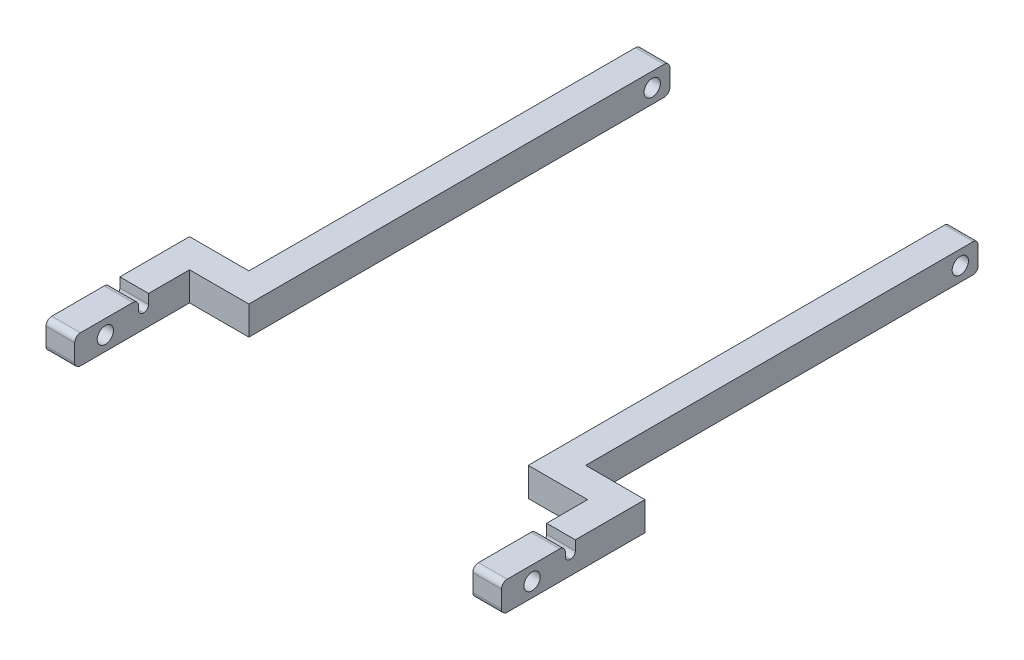
SolidWorks part; units mm, degrees
material "Custom Plastic"
ref_plane "Front Plane" through (0, 0, 0) normal (0, 0, 1) x (1, 0, 0)
ref_plane "Top Plane" through (0, 0, 0) normal (0, 1, 0) x (1, 0, 0)
ref_plane "Right Plane" through (0, 0, 0) normal (1, 0, 0) x (0, 0, -1)
sketch "Sketch2" plane through (0, 0, 0) normal (0, 1, 0) x (1, 0, 0)
  line L0 (130, 280) -> (145, 280)
  line L1 (0, 0) -> (15, 0) construction
  line L2 (0, 75) -> (0, 280)
  line L3 (0, 280) -> (15, 280)
  line L4 (176, 75) -> (176, 280)
  line L6 (46, 280) -> (46, 240)
  line L8 (130, 280) -> (130, 240)
  line L11 (31, 240) -> (31, 280)
  line L15 (145, 240) -> (145, 280)
  line L16 (31, 280) -> (46, 280)
  line L17 (161, 280) -> (176, 280)
  line L25 (130, 240) -> (46, 240)
  line L26 (31, 240) -> (31, 225)
  line L30 (161, 0) -> (176, 0) construction
  line L31 (145, 240) -> (145, 225)
  line L34 (31, 225) -> (145, 225)
  line L35 (15, 280) -> (15, 60)
  line L36 (161, 280) -> (161, 60)
  line L37 (15, 60) -> (-16, 60)
  line L44 (-16, 60) -> (-16, 0)
  line L45 (-16, 0) -> (-31, 0)
  line L46 (-31, 0) -> (-31, 75)
  line L47 (-31, 75) -> (0, 75)
  line L48 (0, 0) -> (0, 60) construction
  line L49 (15, 60) -> (15, 0) construction
  line L50 (0, 60) -> (0, 75) construction
  line L51 (88, 240) -> (88, 0) construction
  line L52 (192, 0) -> (207, 0)
  line L53 (192, 60) -> (192, 0)
  line L54 (161, 60) -> (192, 60)
  line L55 (207, 0) -> (207, 75)
  line L56 (207, 75) -> (176, 75)
  line L57 (176, 0) -> (176, 60) construction
  line L58 (161, 60) -> (161, 0) construction
  line L59 (176, 60) -> (176, 75) construction
  point P6 (31, 260)
  point P36 (0, 0)
  dimension "D2" = 280
  dimension "D3" = 16
  dimension "D4" = 114
  dimension "D6" = 15
  dimension "D7" = 16
  dimension "D8" = 40
  dimension "D9" = 55
  dimension "D10" = 15
  dimension "D11" = 60
  dimension "D12" = 15
  dimension "D14" = 15
  dimension "D17" = 15
  dimension "D18" = 15
extrude "outer legs" add sketch "Sketch2" along normal blind 15
sketch "Sketch6" plane through (0, 0, 0) normal (-1, 0, 0) x (0, 0, 1)
  line L0 (-280, 15) -> (-280, 0) construction
  line L1 (-75, 0) -> (-280, 0) construction
  circle A0 centre (-270.75, 7.5) radius 4.25
  point P4 (0, 0)
  dimension "D1" = 8.5
  dimension "D2" = 9.25
  dimension "D3" = 7.5
sketch "Sketch7" plane through (192, 0, 0) normal (-1, 0, 0) x (0, 0, 1)
  line L3 (0, 15) -> (0, 0) construction
  line L4 (-60, 0) -> (0, 0) construction
  circle A0 centre (-16, 7.5) radius 4.25
  dimension "D1" = 8.5
  dimension "D2" = 16
  dimension "D3" = 7.5
extrude "LOWER DOWEL HOLE" cut sketch "Sketch7" against normal through all both and the other way through all
sketch "Sketch8" plane through (0, 0, 0) normal (-1, 0, 0) x (0, 0, 1)
  line L0 (-75, 15) -> (-280, 15) construction
  line L1 (-38.6, 15) -> (-33.4, 15)
  line L2 (-38.6, 15) -> (-38.6, 7.5)
  line L3 (-38.6, 7.5) -> (-33.4, 7.5)
  line L4 (-33.4, 15) -> (-33.4, 7.5)
  circle A0 centre (-16, 7.5) radius 4.25 construction
  point P6 (-36, 7.5)
  dimension "D1" = 20
  dimension "D2" = 5.2
  dimension "D3" = 7.5
extrude "Cut-Extrude4" cut sketch "Sketch8" against normal through all both and the other way through all
extrude "HINGE HOLE" cut sketch "Sketch6" against normal through all both and the other way through all
fillet "Fillet3" radius 2.5 2 edges at (168.5, 0, -280) (168.5, 15, -280)
fillet "Fillet5" radius 3 1 edges at (-23.5, 15, -33.4)
fillet "Fillet6" radius 3 1 edges at (199.5, 15, -33.4)
fillet "Fillet10" radius 3 2 edges at (-23.5, 0, 0) (-23.5, 15, 0)
fillet "Fillet11" radius 3 2 edges at (199.5, 0, 0) (199.5, 15, 0)
fillet "Fillet12" radius 2.5 2 edges at (-23.5, 7.5, -33.4) (-23.5, 7.5, -38.6)
fillet "Fillet13" radius 2.5 2 edges at (199.5, 7.5, -38.6) (199.5, 7.5, -33.4)
fillet "Fillet14" radius 3 2 edges at (7.5, 0, -280) (7.5, 15, -280)
